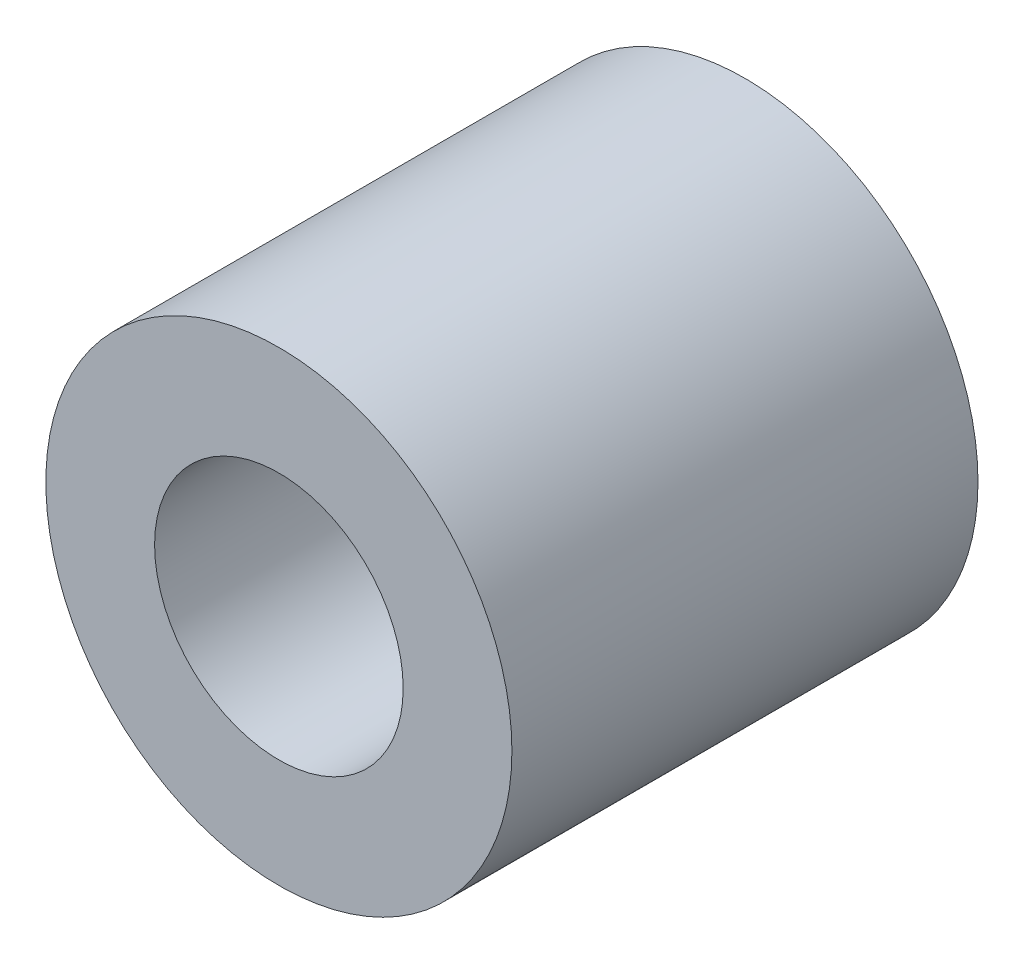
SolidWorks part; units mm, degrees
material "Латунь"
ref_plane "Спереди" through (0, 0, 0) normal (0, 0, 1) x (1, 0, 0)
ref_plane "Сверху" through (0, 0, 0) normal (0, 1, 0) x (1, 0, 0)
ref_plane "Справа" through (0, 0, 0) normal (1, 0, 0) x (0, 0, -1)
sketch "Эскиз7" plane through (0, 0, 0) normal (1, 0, 0) x (0, 0, -1)
  line L1 (0, 0) -> (3, 0)
  line L2 (0, 0) -> (0, 1.4)
  line L3 (0, 1.4) -> (3, 1.4)
  line L4 (3, 0) -> (3, 1.4)
  dimension "D1" = 3
  dimension "D2" = 1.4
revolve "Повернуть1" add sketch "Эскиз7" angle 360 about L1
hole_wizard "Отверстие обработанное метчиком M21" positions "Эскиз8" profile "Эскиз9" tap size "M2" standard "DIN" end condition through all
sketch "Эскиз8" plane through (0, 0, 0) normal (0, 0, 1) x (1, 0, 0)
  point P0 (0, 0)
sketch "Эскиз9" plane through (0, 0, 0) normal (1, 0, 0) x (0, -1, 0)
  line L0 (0, 0) -> (0, 3)
  line L1 (0, 3) -> (0.8, 3)
  line L2 (0.8, 3) -> (0.8, 0)
  line L5 (0.8, 0) -> (0, 0)
  line L11 (0, -6.35) -> (0, 107.95) construction
  dimension "Диаметр проходного сверла" = 1.6
  dimension "Глубина проходного сверла" = 3
cosmetic thread "Отверстие резьбы2" parameters "D2"=2
sketch "Эскиз45" plane through (0, 0, 0) normal (0, 0, 1) x (1, 0, 0)
  line L0 (0, 0) -> (0, 1.4) construction
  line L1 (0, 0.0356) -> (0, 0) construction
  line L2 (0, 0) -> (0.2605, 1.4772) construction
  line L3 (0, 1.5) -> (0, 0) construction
  line L4 (0, 1.5) -> (0, 1.4)
  line L5 (0.2431, 1.3787) -> (0.2605, 1.4772)
  arc A0 (0, 1.5) -> (0.2605, 1.4772) centre (0, 0) cw
  arc A2 (0.2431, 1.3787) -> (0, 1.4) centre (0, 0) ccw
  dimension "D2" = 1.4
  dimension "D3" = 1.5
  dimension "D1" = 10
sketch "Эскиз46" plane through (0, 0, -3) normal (0, 0, -1) x (-1, 0, 0)
  line L0 (0, 0) -> (0.2605, 1.4772) construction
  line L1 (0, 1.5) -> (0, 0) construction
  line L2 (0, 1.5) -> (0, 1.4)
  line L3 (0.2605, 1.4772) -> (0.2431, 1.3787)
  line L4 (0, 0) -> (0, 1.4) construction
  arc A0 (0.2605, 1.4772) -> (0, 1.5) centre (0, 0) ccw
  arc A1 (0.2431, 1.3787) -> (0, 1.4) centre (0, 0) ccw
  arc A2 (0, 1.5) -> (-0.2605, 1.4772) centre (0, 0) ccw construction
  dimension "D2" = 1.4
  dimension "D1" = 10
loft "По сечениям1" [suppressed] add profiles "Эскиз45", "Эскиз46"
pattern_circular "Круговой массив1" [suppressed] count 18 over 360
combine bodies "Соединить1" [suppressed] bodies to combine 107 108 109 110 111 112 113 115 116 117 118 119 120 121 122 123 124 125 114
sketch "Эскиз47" plane through (0, 0, 0) normal (0, 0, 1) x (1, 0, 0)
  circle A0 centre (0, 0) radius 1.4
  circle A1 centre (0, 0) radius 1.5
  dimension "D1" = 3
  dimension "D2" = 2.8
extrude "Бобышка-Вытянуть1" add sketch "Эскиз47" against normal up to surface (3 mm away) up to face at (0.8, 0, -3)
